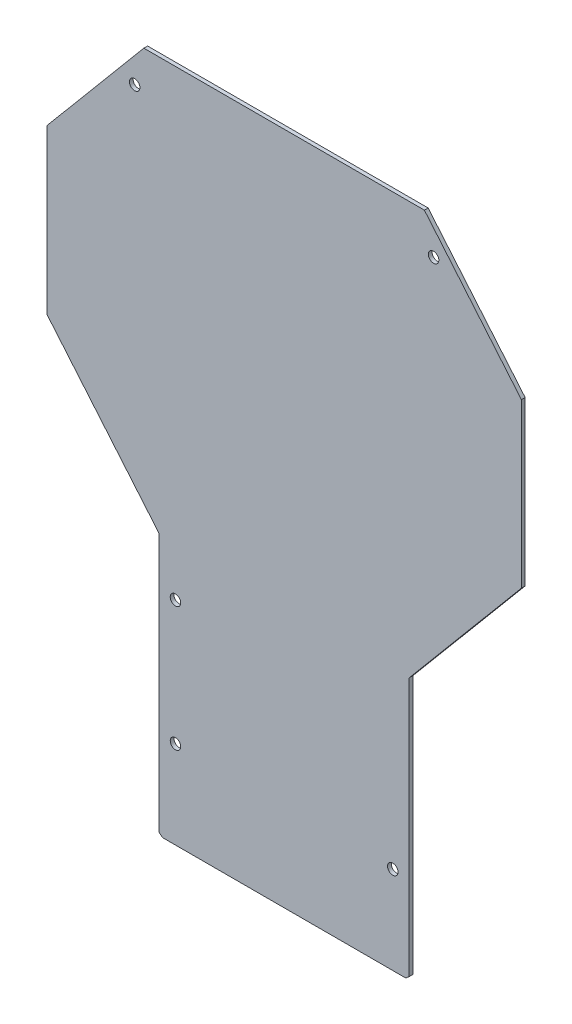
SolidWorks part; units mm, degrees
ref_plane "Plano frontal" through (0, 0, 0) normal (0, 0, 1) x (1, 0, 0)
ref_plane "Plano superior" through (0, 0, 0) normal (0, 1, 0) x (1, 0, 0)
ref_plane "Plano direito" through (0, 0, 0) normal (1, 0, 0) x (0, 0, -1)
sketch "Esboço1" plane through (0, 0, 0) normal (0, 0, 1) x (1, 0, 0)
  line L6 (55.321, 133.8096) -> (-57.007, 133.8096)
  line L7 (-57.007, 133.8096) -> (-95.843, 87.5267)
  line L8 (-95.843, 87.5267) -> (-95.843, 22.1402)
  line L9 (-95.843, 22.1402) -> (-50.843, -31.4887)
  line L10 (-50.843, -31.4887) -> (-50.843, -135.0827)
  line L11 (-50.843, -135.0827) -> (-49.5229, -136.1904)
  line L12 (-49.5229, -136.1904) -> (47.8369, -136.1904)
  line L13 (49.157, -135.0827) -> (47.8369, -136.1904)
  line L14 (49.157, -31.4887) -> (49.157, -135.0827)
  line L15 (94.157, 22.1402) -> (49.157, -31.4887)
  line L16 (94.157, 87.5267) -> (94.157, 22.1402)
  line L17 (55.321, 133.8096) -> (94.157, 87.5267)
  point P16 (-0.843, -136.1904)
  point P17 (-0.843, 133.8096)
extrude "Ressalto-extrusão1" add sketch "Esboço1" along normal blind 1.5
sketch "Esboço2" plane through (0, 0, 1.5) normal (0, 0, 1) x (1, 0, 0)
  line L2 (55.321, 133.8096) -> (-57.007, 133.8096) construction
  line L3 (-49.5229, -136.1904) -> (47.8369, -136.1904) construction
  line L4 (49.157, -135.0827) -> (49.157, -31.4887) construction
  line L5 (-57.007, 133.8096) -> (-95.843, 87.5267) construction
  line L6 (94.157, 87.5267) -> (55.321, 133.8096) construction
  line L9 (-50.843, -31.4887) -> (-50.843, -135.0827) construction
  circle A0 centre (-60.6849, 119.3142) radius 2.1
  circle A1 centre (-44.343, -101.0304) radius 2.1
  circle A2 centre (42.657, -101.0304) radius 2.1
  circle A3 centre (58.999, 119.3142) radius 2.1
  circle A6 centre (-44.343, -51.1904) radius 2.1
  dimension "D2" = 6.5
  dimension "D5" = 6.5
  dimension "D6" = 85
  dimension "D7" = 14.4954
  dimension "D4" = 35.16
  dimension "D10" = 6.5
  dimension "D12" = 35.16
  dimension "D14" = 6.5
  dimension "D11" = 14.4954
  dimension "D15" = 6.5
extrude "Corte-extrusão1" cut sketch "Esboço2" against normal up to next
